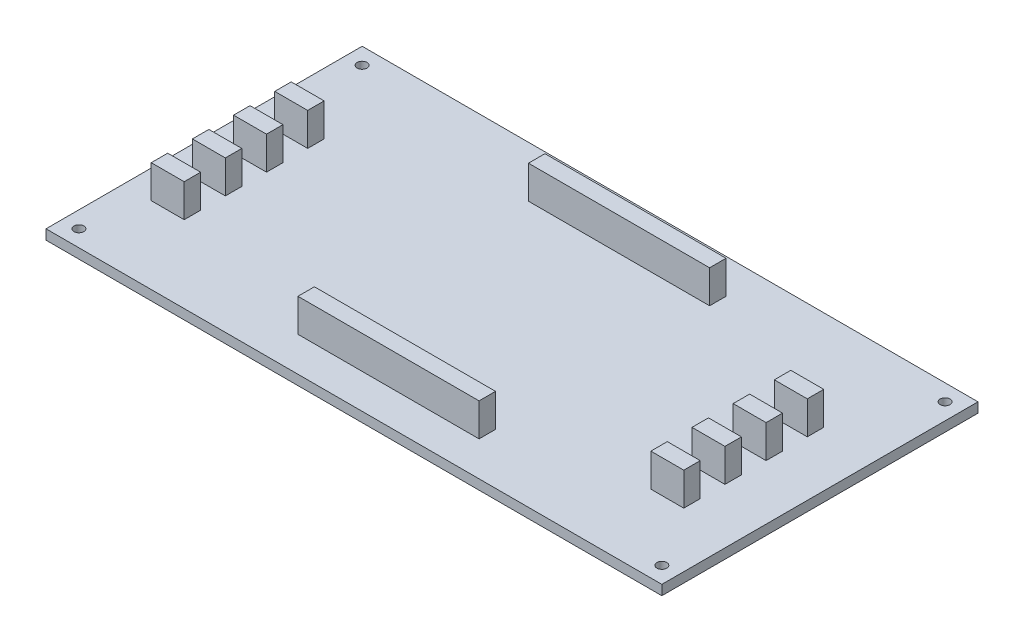
SolidWorks part; units mm, degrees
ref_plane "Face" through (0, 0, 0) normal (0, 0, 1) x (1, 0, 0)
ref_plane "Dessus" through (0, 0, 0) normal (0, 1, 0) x (1, 0, 0)
ref_plane "Droite" through (0, 0, 0) normal (1, 0, 0) x (0, 0, -1)
sketch "Esquisse1" plane through (0, 0, 0) normal (0, 1, 0) x (1, 0, 0)
  line L0 (93.5, 96) -> (93.5, 0) construction
  line L1 (0, 0) -> (187, 0)
  line L2 (0, 0) -> (0, 96)
  line L3 (0, 96) -> (187, 96)
  line L4 (187, 0) -> (187, 96)
  line L5 (0, 48) -> (187, 48) construction
  circle A0 centre (5, 91) radius 1.5
  circle A1 centre (182, 91) radius 1.5
  circle A2 centre (182, 5) radius 1.5
  circle A3 centre (5, 5) radius 1.5
  dimension "D3" = 3
  dimension "D1" = 96
  dimension "D2" = 187
  dimension "D4" = 5
  dimension "D5" = 5
extrude "Extrusion1" add sketch "Esquisse1" along normal blind 3
sketch "Esquisse2" plane through (0, 3, 0) normal (0, 1, 0) x (1, 0, 0)
  line L0 (66, 85.5) -> (66, 10.5) construction
  line L1 (66, 85.5) -> (121, 85.5)
  line L2 (66, 85.5) -> (66, 80.5)
  line L3 (66, 80.5) -> (121, 80.5)
  line L4 (121, 85.5) -> (121, 80.5)
  line L5 (66, 15.5) -> (121, 15.5)
  line L6 (66, 15.5) -> (66, 10.5)
  line L7 (66, 10.5) -> (121, 10.5)
  line L8 (121, 15.5) -> (121, 10.5)
  line L10 (121, 85.5) -> (121, 10.5) construction
  line L12 (93.5, 96) -> (93.5, 0) construction
  line L13 (187, 96) -> (0, 96) construction
  line L14 (0, 0) -> (187, 0) construction
  line L15 (0, 48) -> (187, 48) construction
  line L16 (0, 96) -> (0, 0) construction
  line L17 (187, 0) -> (187, 96) construction
  point P20 (66, 48)
  point P21 (93.5, 80.5)
  dimension "D1" = 65
  dimension "D2" = 5
  dimension "D4" = 55
extrude "Extrusion2" add sketch "Esquisse2" along normal blind 10
sketch "Esquisse4" plane through (0, 3, 0) normal (0, 1, 0) x (1, 0, 0)
  line L0 (160.2951, 65.8623) -> (170.2951, 65.8623)
  line L1 (8.5938, 65.8623) -> (18.5938, 65.8623)
  line L2 (8.5938, 65.8623) -> (8.5938, 60.8623)
  line L3 (8.5938, 60.8623) -> (18.5938, 60.8623)
  line L4 (18.5938, 65.8623) -> (18.5938, 60.8623)
  line L5 (8.5938, 40.8623) -> (18.5938, 40.8623)
  line L6 (8.5938, 40.8623) -> (8.5938, 35.8623)
  line L7 (8.5938, 35.8623) -> (18.5938, 35.8623)
  line L8 (18.5938, 40.8623) -> (18.5938, 35.8623)
  line L9 (8.5938, 28.3623) -> (18.5938, 28.3623)
  line L10 (8.5938, 28.3623) -> (8.5938, 23.3623)
  line L11 (8.5938, 23.3623) -> (18.5938, 23.3623)
  line L12 (18.5938, 28.3623) -> (18.5938, 23.3623)
  line L13 (8.5938, 53.3623) -> (18.5938, 53.3623)
  line L14 (8.5938, 53.3623) -> (8.5938, 48.3623)
  line L15 (8.5938, 48.3623) -> (18.5938, 48.3623)
  line L16 (18.5938, 53.3623) -> (18.5938, 48.3623)
  line L17 (160.2951, 65.8623) -> (160.2951, 60.8623)
  line L18 (160.2951, 60.8623) -> (170.2951, 60.8623)
  line L19 (170.2951, 65.8623) -> (170.2951, 60.8623)
  line L20 (160.2951, 40.8623) -> (170.2951, 40.8623)
  line L21 (160.2951, 40.8623) -> (160.2951, 35.8623)
  line L22 (160.2951, 35.8623) -> (170.2951, 35.8623)
  line L23 (170.2951, 40.8623) -> (170.2951, 35.8623)
  line L24 (160.2951, 28.3623) -> (170.2951, 28.3623)
  line L25 (160.2951, 28.3623) -> (160.2951, 23.3623)
  line L26 (160.2951, 23.3623) -> (170.2951, 23.3623)
  line L27 (170.2951, 28.3623) -> (170.2951, 23.3623)
  line L28 (160.2951, 53.3623) -> (170.2951, 53.3623)
  line L29 (160.2951, 53.3623) -> (160.2951, 48.3623)
  line L30 (160.2951, 48.3623) -> (170.2951, 48.3623)
  line L31 (170.2951, 53.3623) -> (170.2951, 48.3623)
  dimension "D1" = 10
  dimension "D2" = 5
  dimension "D3" = 7.5
  dimension "D4" = 7.5
  dimension "D5" = 7.5
  dimension "D6" = 10
  dimension "D7" = 5
  dimension "D8" = 7.5
  dimension "D9" = 7.5
  dimension "D10" = 7.5
extrude "Extrusion4" add sketch "Esquisse4" along normal blind 10
